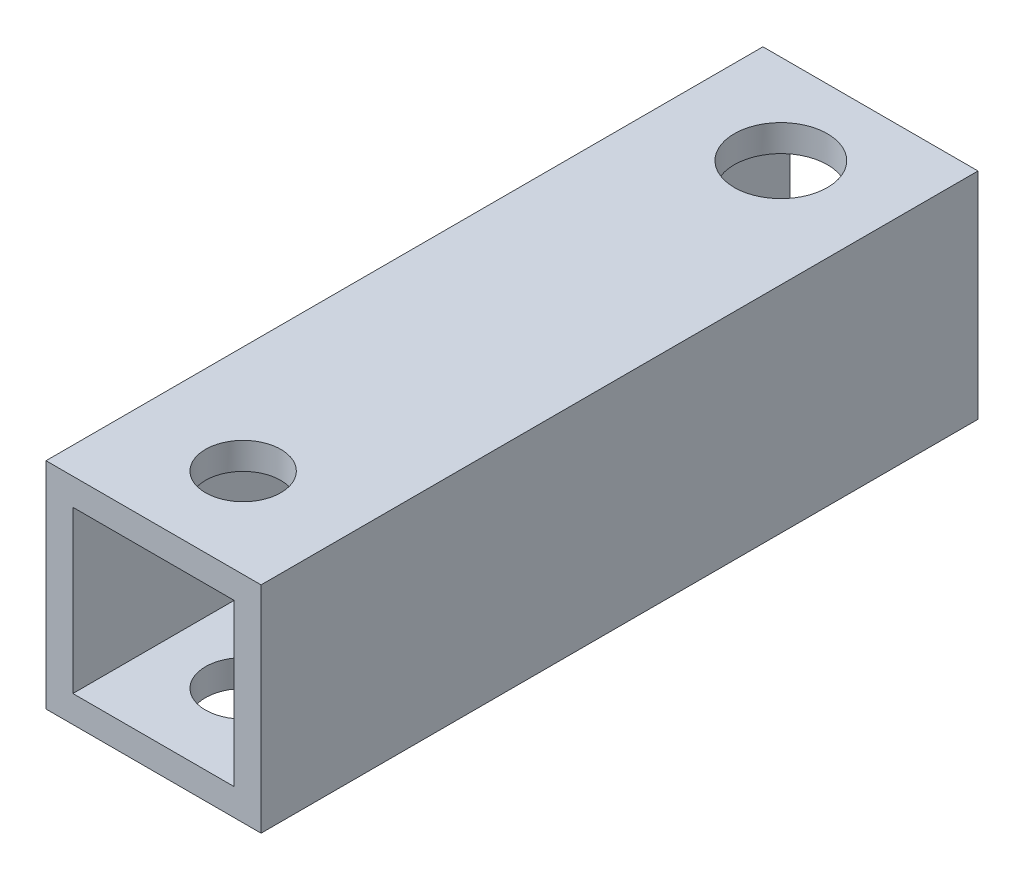
SolidWorks part; units mm, degrees
ref_plane "正面" through (0, 0, 0) normal (0, 0, 1) x (1, 0, 0)
ref_plane "平面" through (0, 0, 0) normal (0, 1, 0) x (1, 0, 0)
ref_plane "右側面" through (0, 0, 0) normal (1, 0, 0) x (0, 0, -1)
sketch "ｽｹｯﾁ1" plane through (0, 0, 0) normal (0, 0, 1) x (1, 0, 0)
  line L1 (-4.5, 4.5) -> (4.5, 4.5)
  line L2 (-4.5, 4.5) -> (-4.5, -4.5)
  line L3 (-4.5, -4.5) -> (4.5, -4.5)
  line L4 (4.5, 4.5) -> (4.5, -4.5)
  line L5 (-4.5, 4.5) -> (4.5, -4.5) construction
  line L6 (-4.5, -4.5) -> (4.5, 4.5) construction
  line L7 (-6, 6) -> (6, 6)
  line L8 (-6, 6) -> (-6, -6)
  line L9 (-6, -6) -> (6, -6)
  line L10 (6, 6) -> (6, -6)
  line L11 (-6, 6) -> (6, -6) construction
  line L12 (-6, -6) -> (6, 6) construction
  point P0 (0, 0)
  point P6 (0, 0)
  dimension "D1" = 12
  dimension "D2" = 12
  dimension "D3" = 9
  dimension "D4" = 9
extrude "ﾎﾞｽ - 押し出し1" add sketch "ｽｹｯﾁ1" along normal blind 40
sketch "ｽｹｯﾁ2" plane through (0, 6, 0) normal (0, 1, 0) x (1, 0, 0)
  line L0 (0, 0) -> (0, -5)
  line L1 (6, 0) -> (-6, 0) construction
  line L2 (0, -40) -> (0, -35)
  line L3 (6, -40) -> (-6, -40) construction
  circle A0 centre (0, -5) radius 2.6
  circle A1 centre (0, -35) radius 2.1
  dimension "D3" = 5.2
  dimension "D4" = 4.2
  dimension "D1" = 5
  dimension "D2" = 5
extrude "ｶｯﾄ - 押し出し1" cut sketch "ｽｹｯﾁ2" against normal blind 30
